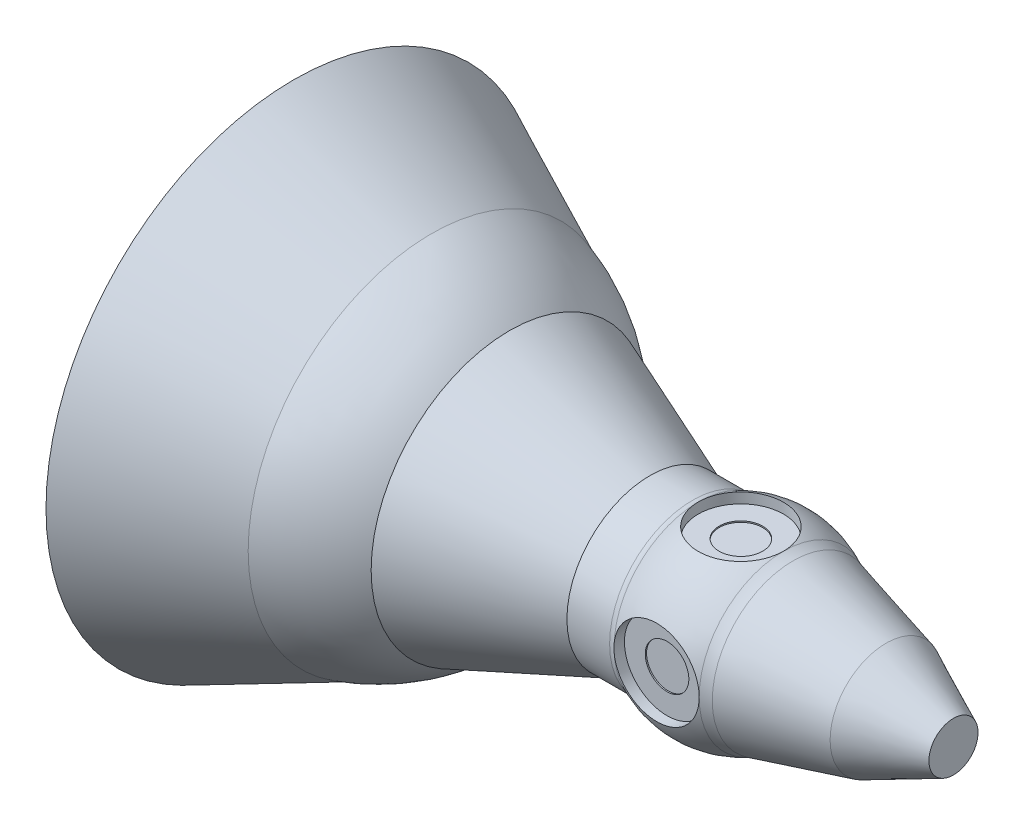
SolidWorks part; units mm, degrees
ref_plane "Plano frontal" through (0, 0, 0) normal (0, 0, 1) x (1, 0, 0)
ref_plane "Plano superior" through (0, 0, 0) normal (0, 1, 0) x (1, 0, 0)
ref_plane "Plano direito" through (0, 0, 0) normal (1, 0, 0) x (0, 0, -1)
sketch "Esboço1" plane through (0, 0, 0) normal (0, 0, 1) x (1, 0, 0)
  line L0 (0, 0) -> (0, 2210.2124) construction
  line L1 (0, 0) -> (3317.3997, 0) construction
  line L2 (3317.3997, 0) -> (3317.3997, 383.5)
  line L3 (3317.3997, 383.5) -> (2265.3997, 873)
  line L4 (2265.3997, 873) -> (813.3997, 1260)
  line L5 (0, -29.8386) -> (665, 1315.8122) construction
  line L6 (0, -29.8386) -> (-665, 1315.8122) construction
  line L7 (-753.6076, 1295.1127) -> (-1420, 1295.1127)
  line L8 (-6980, 3864) -> (-6980, 0)
  line L9 (-6980, 0) -> (3317.3997, 0)
  line L10 (-1420, 1295.1127) -> (-3610, 2160)
  line L11 (-4829, 2860) -> (-6980, 3864)
  arc A0 (665, 1315.8122) -> (-665, 1315.8122) centre (0, -29.8386) ccw
  arc A1 (813.3997, 1260) -> (665, 1315.8122) centre (1019.4304, 2033.0145) cw
  arc A2 (-753.6076, 1295.1127) -> (-665, 1315.8122) centre (-753.6076, 1495.1127) ccw
  arc A3 (-3610, 2160) -> (-4829, 2860) centre (-5637.2528, 41.0847) ccw
  point P17 (-4829, 2860)
  dimension "D1" = 800
  dimension "D7" = 1501
  dimension "D9" = 200
  dimension "D11" = 3610
  dimension "D14" = 2160
  dimension "D15" = 5865
  dimension "D2" = 767
  dimension "D3" = 1746
  dimension "D4" = 1052
  dimension "D5" = 2520
  dimension "D6" = 1452
  dimension "D8" = 1330
  dimension "D10" = 1420
  dimension "D12" = 4829
  dimension "D13" = 2860
  dimension "D16" = 3864
  dimension "D17" = 6980
revolve "Revolução1" add sketch "Esboço1" angle 360 about L9
sketch "Esboço2" plane through (0, 0, 0) normal (1, 0, 0) x (0, 0, -1)
  line L0 (0, 0) -> (0, 3522.5113) construction
  line L1 (665, 1312.2846) -> (665, 1152.2846)
  line L2 (665, 1152.2846) -> (340, 1152.2846)
  line L3 (0, 1132.2846) -> (0, 1471.1614)
  line L4 (340, 1152.2846) -> (340, 1132.2846)
  line L5 (340, 1132.2846) -> (0, 1132.2846)
  line L6 (0, 1471.1614) -> (0, 1794.4974)
  line L7 (0, 1794.4974) -> (665, 1794.4974)
  line L8 (665, 1794.4974) -> (665, 1312.2846)
  circle A0 centre (0, 0) radius 1471.1614 construction
  arc A1 (665, 1312.2846) -> (0, 1471.1614) centre (0, 0) ccw construction
  dimension "D1" = 1330
  dimension "D2" = 160
  dimension "D3" = 20
  dimension "D4" = 680
revolve "Corte-Revolução7" cut sketch "Esboço2" angle 360 about L0
pattern_circular "PadrãoCircular1" count 4 over 360 about axis through (0, 0, 0) along (1, 0, 0) of "Corte-Revolução7"
